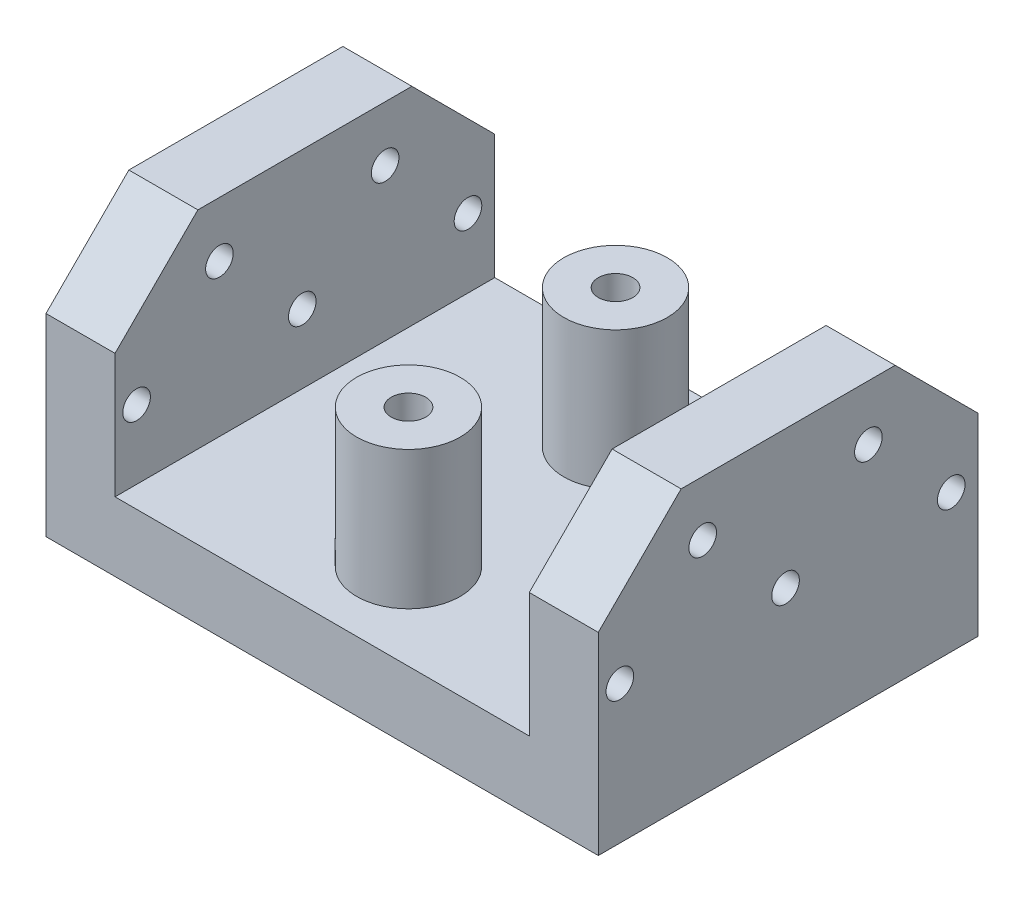
SolidWorks part; units mm, degrees
material "ABS"
ref_plane "Front Plane" through (0, 0, 0) normal (0, 0, 1) x (1, 0, 0)
ref_plane "Top Plane" through (0, 0, 0) normal (0, 1, 0) x (1, 0, 0)
ref_plane "Right Plane" through (0, 0, 0) normal (1, 0, 0) x (0, 0, -1)
sketch "Sketch1" plane through (0, 0, 0) normal (0, 1, 0) x (1, 0, 0)
  line L1 (-40, -27.5) -> (40, -27.5)
  line L2 (-40, -27.5) -> (-40, 27.5)
  line L3 (-40, 27.5) -> (40, 27.5)
  line L4 (40, -27.5) -> (40, 27.5)
  line L5 (-40, -27.5) -> (40, 27.5) construction
  line L6 (-40, 27.5) -> (40, -27.5) construction
  point P0 (0, 0)
  dimension "D1" = 80
  dimension "D2" = 55
extrude "Boss-Extrude1" add sketch "Sketch1" along normal blind 10
sketch "Sketch2" plane through (0, 10, 0) normal (0, 1, 0) x (1, 0, 0)
  line L0 (-40, -27.5) -> (40, -27.5) construction
  line L1 (-40, 27.5) -> (-30, 27.5)
  line L2 (-40, 27.5) -> (-40, -27.5)
  line L3 (-40, -27.5) -> (-30, -27.5)
  line L4 (-30, 27.5) -> (-30, -27.5)
  line L6 (40, 27.5) -> (30, 27.5)
  line L7 (40, 27.5) -> (40, -27.5)
  line L8 (40, -27.5) -> (30, -27.5)
  line L9 (30, 27.5) -> (30, -27.5)
  dimension "D1" = 10
  dimension "D2" = 10
extrude "Boss-Extrude2" add sketch "Sketch2" along normal blind 30
sketch "Sketch3" plane through (-40, 0, 0) normal (-1, 0, 0) x (0, 0, 1)
  line L0 (-24.4564, 20) -> (25.208, 20) construction
  line L1 (-27.5, 0) -> (27.5, 0) construction
  line L2 (-23.6242, 32) -> (24.3758, 32) construction
  circle A0 centre (-23.6242, 20) radius 2
  circle A1 centre (0.3758, 20) radius 2
  circle A2 centre (24.3758, 20) radius 2
  circle A3 centre (-11.6242, 32) radius 2
  circle A4 centre (12.3758, 32) radius 2
  dimension "D1" = 4
  dimension "D2" = 4
  dimension "D3" = 4
  dimension "D8" = 4
  dimension "D9" = 4
  dimension "D4" = 24
  dimension "D5" = 24
  dimension "D6" = 20
  dimension "D7" = 12
  dimension "D10" = 12
  dimension "D11" = 12
extrude "Cut-Extrude1" cut sketch "Sketch3" against normal through all
sketch "Sketch4" plane through (0, 0, 0) normal (0, -1, 0) x (1, 0, 0)
  line L0 (-29.1816, 0) -> (32.7136, 0) construction
  line L1 (0, 21.9913) -> (0, -22.58) construction
  circle A0 centre (0, 15) radius 2.5
  circle A1 centre (0, -15) radius 2.5
  dimension "D1" = 5
  dimension "D2" = 5
  dimension "D3" = 15
  dimension "D4" = 15
extrude "Cut-Extrude2" cut sketch "Sketch4" against normal blind 30
sketch "Sketch5" plane through (0, 10, 0) normal (0, 1, 0) x (1, 0, 0)
  circle A0 centre (0, -15) radius 2.5 construction
  circle A1 centre (0, 15) radius 2.5 construction
  circle A2 centre (0, -15) radius 2.5
  circle A3 centre (0, 15) radius 2.5
  circle A4 centre (0, 15) radius 7.5
  circle A5 centre (0, -15) radius 7.5
  dimension "D1" = 15
  dimension "D2" = 15
extrude "Boss-Extrude3" add sketch "Sketch5" along normal blind 20
sketch "Sketch6" plane through (0, 0, 0) normal (0, -1, 0) x (1, 0, 0)
  line L0 (0, 15) -> (0, 10.75) construction
  line L1 (0, -15) -> (0, -10.75) construction
  line L2 (-10.25, 10.75) -> (10.25, 10.75)
  line L3 (-10.25, -10.75) -> (10.25, -10.75)
  line L4 (-10.25, 10.75) -> (-10.25, 7.5)
  line L5 (-10.25, 7.5) -> (10.25, 7.5)
  line L6 (10.25, 7.5) -> (10.25, 10.75)
  line L7 (-10.25, -10.75) -> (-10.25, -7.5)
  line L8 (-10.25, -7.5) -> (10.25, -7.5)
  line L9 (10.25, -7.5) -> (10.25, -10.75)
  dimension "D1" = 4.25
  dimension "D2" = 4.25
  dimension "D3" = 20.5
  dimension "D4" = 20.5
  dimension "D5" = 10.25
  dimension "D6" = 10.25
  dimension "D7" = 3.25
  dimension "D8" = 3.25
extrude "Cut-Extrude3" cut sketch "Sketch6" against normal blind 5
sketch "Sketch7" plane through (40, 0, 0) normal (1, 0, 0) x (0, 0, -1)
  line L0 (-27.5, 28) -> (-15.5, 40)
  line L1 (-27.5, 40) -> (-27.5, 0) construction
  line L2 (-27.5, 40) -> (27.5, 40) construction
  line L3 (15.5, 40) -> (27.5, 28)
  line L4 (27.5, 40) -> (27.5, 0) construction
  line L5 (-27.5, 28) -> (-27.5, 40)
  line L6 (-27.5, 40) -> (-15.5, 40)
  line L7 (15.5, 40) -> (27.5, 40)
  line L8 (27.5, 40) -> (27.5, 28)
  dimension "D1" = 12
  dimension "D2" = 12
  dimension "D3" = 12
extrude "Cut-Extrude4" cut sketch "Sketch7" against normal through all
